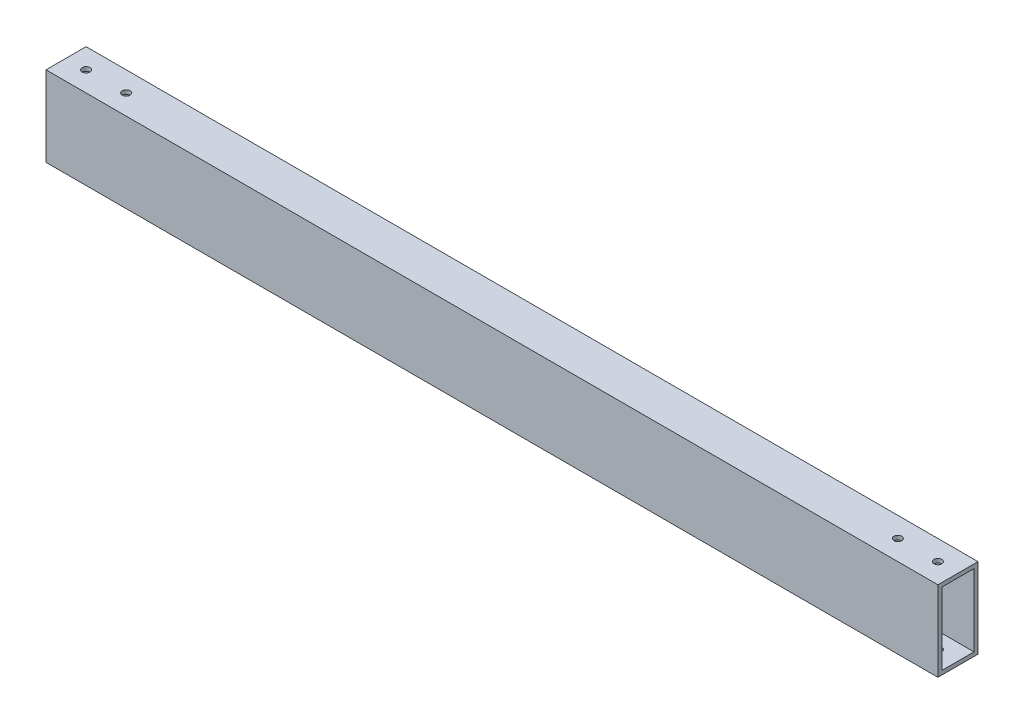
SolidWorks part; units mm, degrees
ref_plane "Front Plane" through (0, 0, 0) normal (0, 0, 1) x (1, 0, 0)
ref_plane "Top Plane" through (0, 0, 0) normal (0, 1, 0) x (1, 0, 0)
ref_plane "Right Plane" through (0, 0, 0) normal (1, 0, 0) x (0, 0, -1)
sketch "Sketch1" plane through (0, 0, 0) normal (1, 0, 0) x (0, 0, -1)
  line L1 (-12.7, -25.4) -> (12.7, -25.4)
  line L2 (-12.7, -25.4) -> (-12.7, 25.4)
  line L3 (-12.7, 25.4) -> (12.7, 25.4)
  line L4 (12.7, -25.4) -> (12.7, 25.4)
  line L5 (-12.7, -25.4) -> (12.7, 25.4) construction
  line L6 (-12.7, 25.4) -> (12.7, -25.4) construction
  point P0 (0, 0)
  dimension "D1" = 25.4
  dimension "D2" = 50.8
extrude "Extrude-Thin1" add sketch "Sketch1" along normal mid plane 565.15 thin thin type one direction reverse wall 2.54
sketch "Sketch2" plane through (0, 25.4, 0) normal (0, 1, 0) x (1, 0, 0)
  line L0 (-282.575, 12.7) -> (-282.575, -12.7) construction
  line L1 (282.575, 12.7) -> (282.575, -12.7) construction
  circle A0 centre (-269.875, 0) radius 2.4765
  circle A1 centre (-244.475, 0) radius 2.4765
  circle A2 centre (269.875, 0) radius 2.4765
  circle A3 centre (244.475, 0) radius 2.4765
  dimension "D1" = 25.4
  dimension "D2" = 25.4
  dimension "D3" = 12.7
  dimension "D4" = 12.7
extrude "Cut-Extrude1" cut sketch "Sketch2" against normal through all
